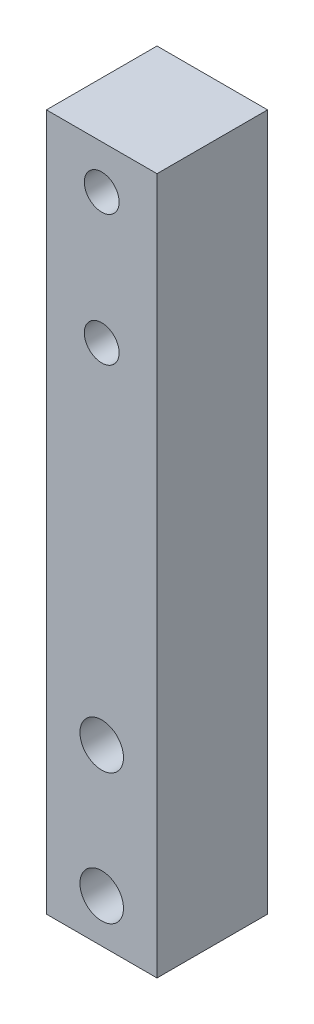
SolidWorks part; units mm, degrees
ref_plane "Front" through (0, 0, 0) normal (0, 0, 1) x (1, 0, 0)
ref_plane "Top" through (0, 0, 0) normal (0, 1, 0) x (1, 0, 0)
ref_plane "Right" through (0, 0, 0) normal (1, 0, 0) x (0, 0, -1)
sketch "Sketch1" plane through (0, 0, 0) normal (0, 0, 1) x (1, 0, 0)
  line L0 (0, 80) -> (0, 0)
  line L1 (0, 0) -> (12.7, 0)
  line L2 (12.7, 0) -> (12.7, 80)
  line L3 (12.7, 80) -> (0, 80)
  dimension "D1" = 12.7
  dimension "D2" = 80
extrude "Boss-Extrude1" add sketch "Sketch1" along normal blind 12.7
sketch "Sketch2" plane through (0, 0, 0) normal (0, 0, 1) x (1, 0, 0)
  line L0 (0, 0) -> (12.7, 0) construction
  line L2 (12.7, 0) -> (12.7, 80) construction
  circle A0 centre (6.35, 5) radius 2.5
  circle A1 centre (6.35, 20) radius 2.5
  circle A2 centre (6.35, 60) radius 2
  circle A3 centre (6.35, 75) radius 2
  dimension "D6" = 4
  dimension "D7" = 5
  dimension "D1" = 15
  dimension "D2" = 15
  dimension "D3" = 40
  dimension "D4" = 5
  dimension "D5" = 6.35
extrude "Cut-Extrude1" cut sketch "Sketch2" along normal through all
